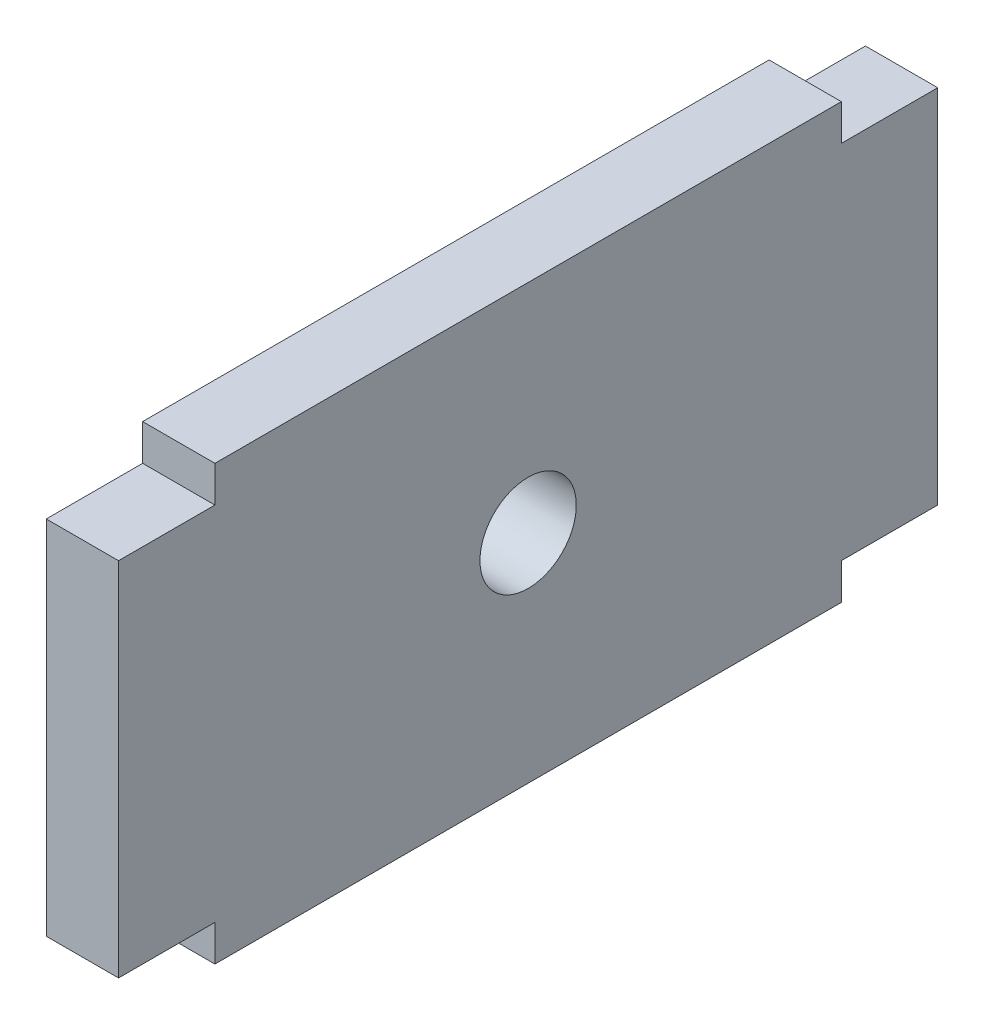
SolidWorks part; units mm, degrees
ref_plane "Front Plane" through (0, 0, 0) normal (0, 0, 1) x (1, 0, 0)
ref_plane "Top Plane" through (0, 0, 0) normal (0, 1, 0) x (1, 0, 0)
ref_plane "Right Plane" through (0, 0, 0) normal (1, 0, 0) x (0, 0, -1)
sketch "Sketch1" plane through (0, 0, 0) normal (1, 0, 0) x (0, 0, -1)
  line L0 (-9.8322, 2.4231) -> (-13.8322, 2.4231)
  line L1 (-9.8322, 3.9231) -> (16.1678, 3.9231)
  line L2 (-9.8322, 3.9231) -> (-9.8322, 2.4231)
  line L3 (-9.8322, -14.0769) -> (16.1678, -14.0769)
  line L4 (16.1678, 3.9231) -> (16.1678, 2.4231)
  line L5 (-13.8322, 2.4231) -> (-13.8322, -12.5769)
  line L6 (-13.8322, -12.5769) -> (-9.8322, -12.5769)
  line L7 (3.1678, 3.9231) -> (3.1678, -1.7158) construction
  line L8 (20.1678, -12.5769) -> (16.1678, -12.5769)
  line L9 (20.1678, 2.4231) -> (20.1678, -12.5769)
  line L10 (16.1678, 2.4231) -> (20.1678, 2.4231)
  line L11 (-9.8322, -12.5769) -> (-9.8322, -14.0769)
  line L12 (16.1678, -12.5769) -> (16.1678, -14.0769)
  dimension "D1" = 26
  dimension "D2" = 18
  dimension "D3" = 4
  dimension "D4" = 15
  dimension "D5" = 1.5
extrude "Boss-Extrude1" add sketch "Sketch1" along normal blind 3
sketch "Sketch2" plane through (0, 0, 0) normal (-1, 0, 0) x (0, 0, 1)
  line L0 (-20.1678, -5.0769) -> (-12.201, -5.0769) construction
  line L1 (-20.1678, -12.5769) -> (-20.1678, 2.4231) construction
  line L2 (-3.1678, 3.9231) -> (-3.1678, 0) construction
  line L3 (-16.1678, 3.9231) -> (9.8322, 3.9231) construction
  circle A0 centre (-3.1678, -5.0769) radius 2
  dimension "D1" = 4
extrude "Cut-Extrude1" cut sketch "Sketch2" against normal blind 3
